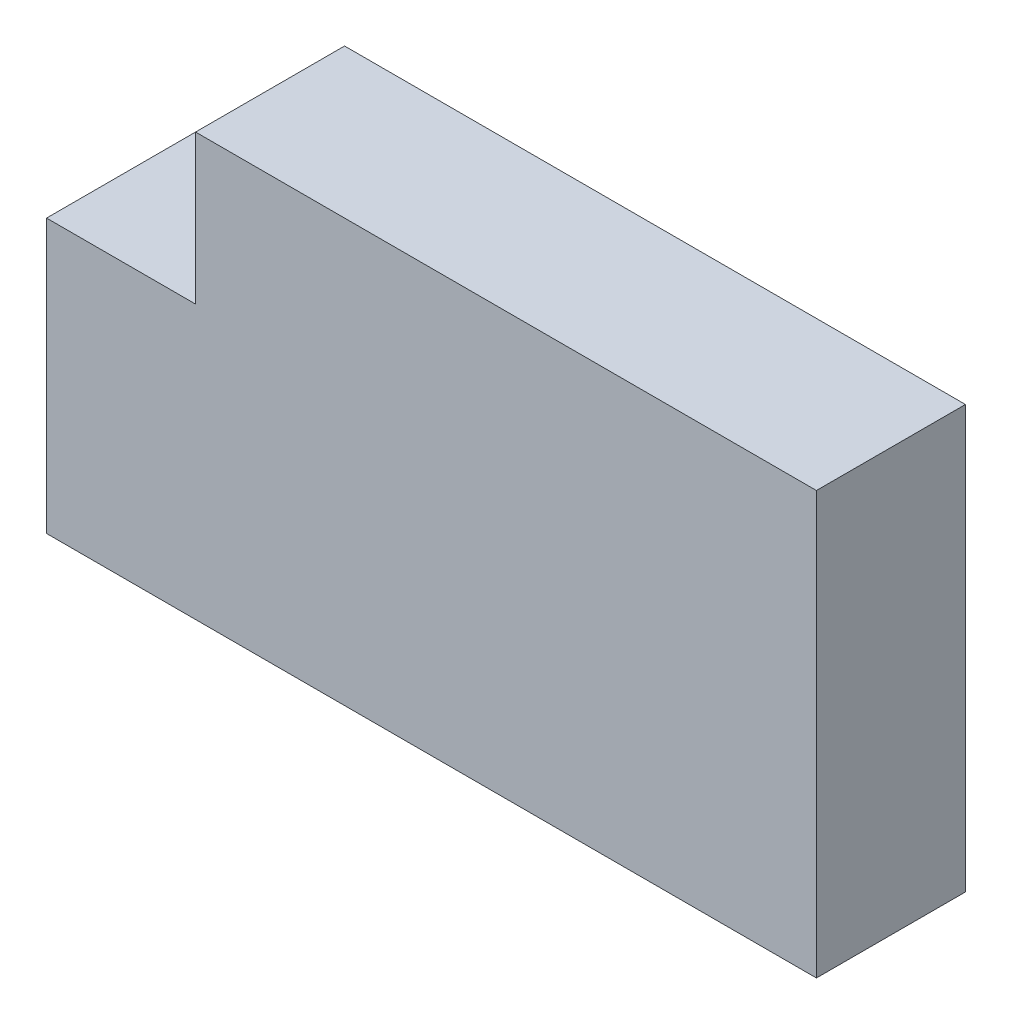
SolidWorks part; units mm, degrees
ref_plane "Plano frontal" through (0, 0, 0) normal (0, 0, 1) x (1, 0, 0)
ref_plane "Plano superior" through (0, 0, 0) normal (0, 1, 0) x (1, 0, 0)
ref_plane "Plano direito" through (0, 0, 0) normal (1, 0, 0) x (0, 0, -1)
sketch "Esboço1" plane through (0, 0, 0) normal (0, 0, 1) x (1, 0, 0)
  line L1 (0, 0) -> (31, 0)
  line L2 (0, 0) -> (0, 17)
  line L3 (0, 17) -> (31, 17)
  line L5 (0, 17) -> (6, 17)
  line L6 (0, 17) -> (0, 11)
  line L7 (0, 11) -> (6, 11)
  line L8 (6, 17) -> (6, 11)
  line L12 (31, 17) -> (31, 0)
  dimension "D1" = 17
  dimension "D2" = 31
  dimension "D3" = 6
extrude "Ressalto-extrusão1" add sketch "Esboço1" along normal blind 6
